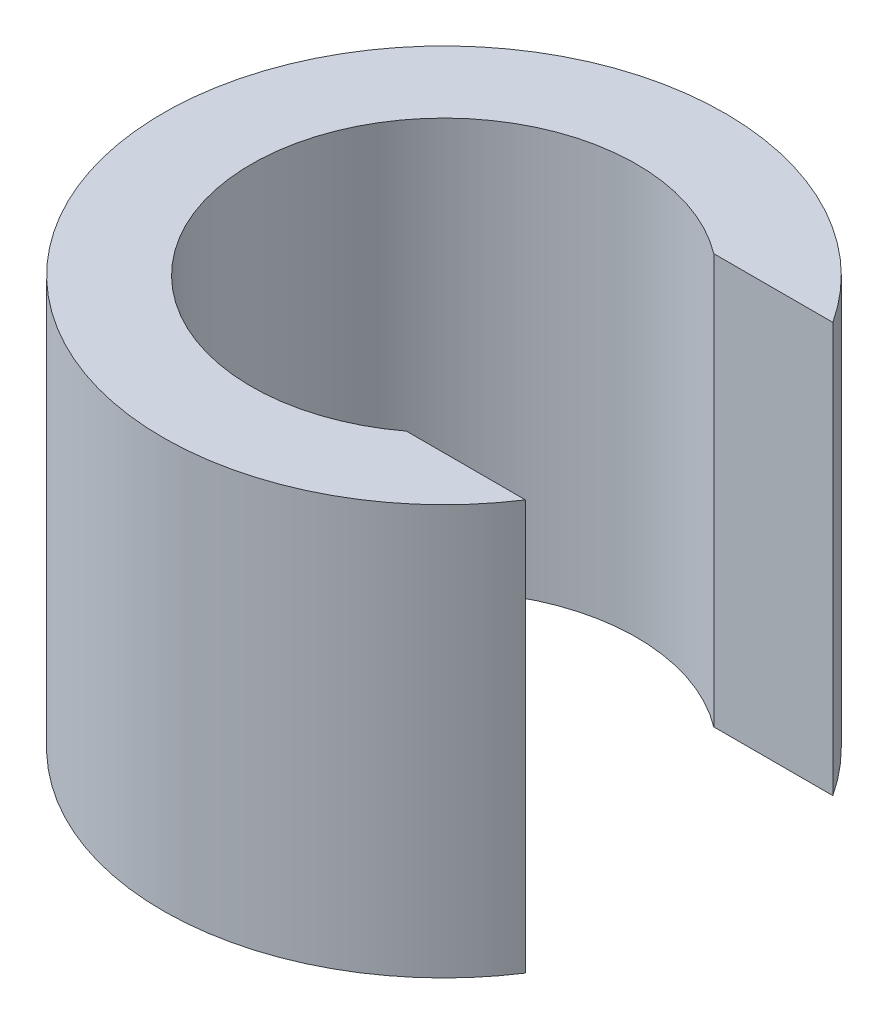
SolidWorks part; units mm, degrees
ref_plane "Front Plane" through (0, 0, 0) normal (0, 0, 1) x (1, 0, 0)
ref_plane "Top Plane" through (0, 0, 0) normal (0, 1, 0) x (1, 0, 0)
ref_plane "Right Plane" through (0, 0, 0) normal (1, 0, 0) x (0, 0, -1)
sketch "Sketch1" plane through (0, 0, 0) normal (0, 1, 0) x (1, 0, 0)
  line L0 (7.1965, 9.525) -> (14.5754, 9.525)
  line L2 (14.5754, -9.525) -> (7.1965, -9.525)
  arc A0 (14.5754, 9.525) -> (14.5754, -9.525) centre (0, 0) ccw
  arc A1 (7.1965, 9.525) -> (7.1965, -9.525) centre (0, 0) ccw
  dimension "D1" = 34.8234
  dimension "D2" = 23.876
  dimension "D3" = 19.05
extrude "Boss-Extrude1" add sketch "Sketch1" along normal blind 25.4
